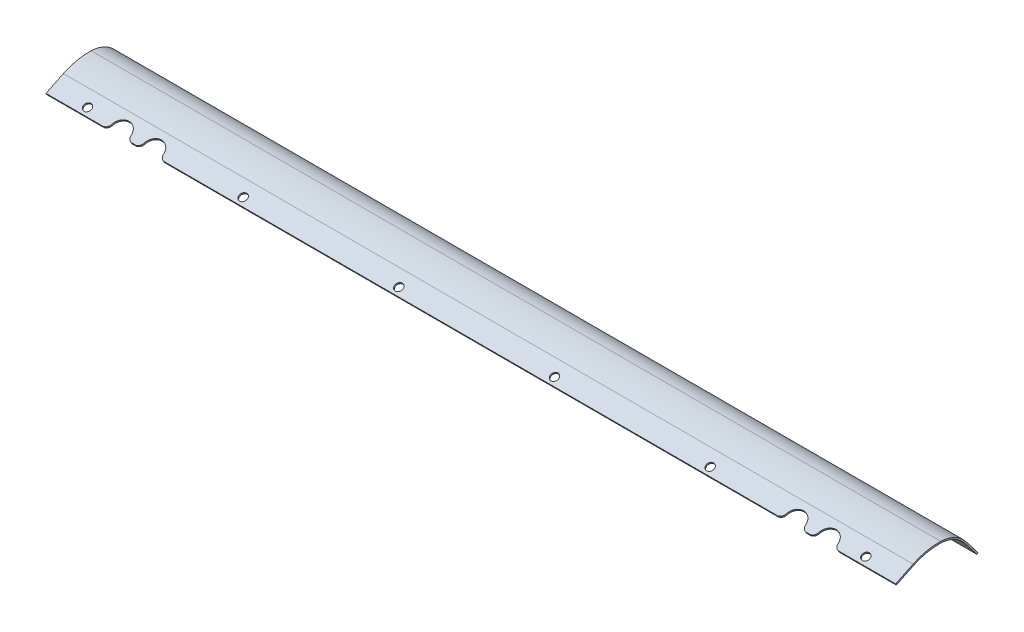
SolidWorks part; units mm, degrees
ref_plane "Front Plane" through (0, 0, 0) normal (0, 0, 1) x (1, 0, 0)
ref_plane "Top Plane" through (0, 0, 0) normal (0, 1, 0) x (1, 0, 0)
ref_plane "Right Plane" through (0, 0, 0) normal (1, 0, 0) x (0, 0, -1)
sketch "Sketch1" plane through (0, 0, 0) normal (1, 0, 0) x (0, 0, -1)
  line L0 (0, 0) -> (8.544, 4.1406)
  line L1 (34.4623, 0.6882) -> (40.3043, -6.8349)
  line L2 (0, 0) -> (0.3323, -0.6857)
  line L3 (0.3323, -0.6857) -> (8.8763, 3.4549)
  line L4 (33.8604, 0.2208) -> (39.7024, -7.3023)
  line L5 (39.7024, -7.3023) -> (40.3043, -6.8349)
  line L6 (8.8763, 3.4549) -> (21.9412, 6.263) construction
  line L7 (8.8763, 3.4549) -> (21.9412, 6.263) construction
  line L8 (22.1147, 7.005) -> (8.544, 4.1406) construction
  line L9 (33.8604, 0.2208) -> (21.9412, 6.263) construction
  line L10 (22.1147, 7.005) -> (34.4623, 0.6882) construction
  line L11 (8.544, 4.1406) -> (8.8763, 3.4549) construction
  line L12 (33.8604, 0.2208) -> (34.4623, 0.6882) construction
  line L13 (139.3957, -135.6843) -> (33.8604, 0.2208) construction
  arc A0 (8.544, 4.1406) -> (22.1147, 7.005) centre (21.1008, -21.7701) cw
  arc A1 (8.8763, 3.4549) -> (21.9412, 6.263) centre (21.1577, -21.8874) cw
  arc A2 (21.9412, 6.263) -> (33.8604, 0.2208) centre (21.506, -9.3729) cw
  arc A3 (22.1147, 7.005) -> (34.4623, 0.6882) centre (21.5385, -9.3476) cw
  dimension "D2" = 39.3701
  dimension "D6" = 6.6166
  dimension "D1" = 0.762
  dimension "D3" = 9.525
  dimension "D4" = 9.525
  dimension "D5" = 101.975
extrude "Boss-Extrude1" add sketch "Sketch1" along normal blind 415.925
sketch "Sketch2" plane through (0, 16.9532, -21.8319) normal (0, 0.6133, -0.7898) x (-1, 0, 0)
  line L0 (-415.925, -30.1182) -> (0, -30.1182) construction
  line L2 (-415.925, -30.1182) -> (-415.925, -20.5932) construction
  circle A1 centre (-398.4625, -26.8927) radius 1.905
  circle A2 centre (-322.2625, -26.8927) radius 1.905
  circle A3 centre (-246.0625, -26.8927) radius 1.905
  circle A4 centre (-169.8625, -26.8927) radius 1.905
  circle A5 centre (-93.6625, -26.8927) radius 1.905
  circle A6 centre (-17.4625, -26.8927) radius 1.905
  circle A7 centre (-381, -28.4802) radius 4.7625
  circle A8 centre (-365.125, -28.4802) radius 4.7625
  circle A9 centre (-50.8, -28.4802) radius 4.7625
  circle A10 centre (-34.925, -28.4802) radius 4.7625
  dimension "D1" = 3.81
  dimension "D3" = 17.4625
  dimension "D6" = 9.525
  dimension "D7" = 9.525
  dimension "D10" = 1.5875
  dimension "D11" = 1.5875
  dimension "D13" = 15.875
  dimension "D2" = 3.2255
  dimension "D5" = 76.2
  dimension "D8" = 15.875
  dimension "D9" = 17.4625
  dimension "D12" = 17.4625
  dimension "D4" = 6
extrude "Cut-Extrude1" cut sketch "Sketch2" against normal through all
sketch "Sketch3" plane through (0, 0, 0) normal (0, 0.8999, 0.4361) x (1, 0, 0)
  line L0 (415.925, 0) -> (0, 0) construction
  circle A1 centre (398.4625, 3.175) radius 1.905
  circle A2 centre (322.2625, 3.175) radius 1.905
  circle A3 centre (246.0625, 3.175) radius 1.905
  circle A4 centre (169.8625, 3.175) radius 1.905
  circle A5 centre (93.6625, 3.175) radius 1.905
  circle A6 centre (17.4625, 3.175) radius 1.905
  circle A7 centre (365.125, 1.5875) radius 4.7625
  circle A8 centre (381, 1.5875) radius 4.7625
  circle A9 centre (34.925, 1.5875) radius 4.7625
  circle A10 centre (50.8, 1.5875) radius 4.7625
  dimension "D1" = 3.81
  dimension "D3" = 17.4625
  dimension "D5" = 76.2
  dimension "D6" = 9.525
  dimension "D7" = 9.525
  dimension "D11" = 9.525
  dimension "D14" = 1.5875
  dimension "D2" = 3.175
  dimension "D8" = 1.5875
  dimension "D9" = 15.875
  dimension "D10" = 17.4625
  dimension "D12" = 15.875
  dimension "D13" = 17.4625
  dimension "D4" = 6
extrude "Cut-Extrude2" cut sketch "Sketch3" against normal through all
fillet "Fillet1" radius 2.54 16 edges at (360.653, -7.0686, -40.0033) (369.597, -7.0686, -40.0033) (376.528, -7.0686, -40.0033) (385.472, -7.0686, -40.0033) (30.453, -7.0686, -40.0033) (39.397, -7.0686, -40.0033) (46.328, -7.0686, -40.0033) (55.272, -7.0686, -40.0033) (55.2901, -0.3429, -0.1662) (46.3099, -0.3429, -0.1662) (39.4151, -0.3429, -0.1662) (30.4349, -0.3429, -0.1662) (385.4901, -0.3429, -0.1662) (376.5099, -0.3429, -0.1662) (369.6151, -0.3429, -0.1662) (360.6349, -0.3429, -0.1662)
